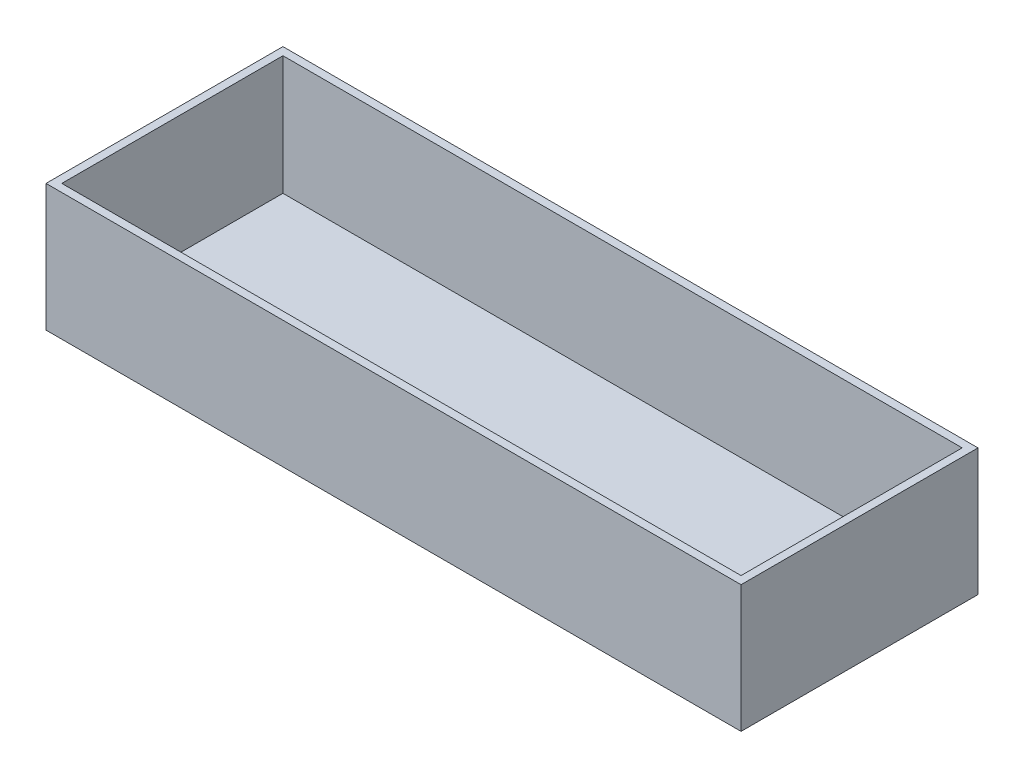
SolidWorks part; units mm, degrees
ref_plane "Front Plane" through (0, 0, 0) normal (0, 0, 1) x (1, 0, 0)
ref_plane "Top Plane" through (0, 0, 0) normal (0, 1, 0) x (1, 0, 0)
ref_plane "Right Plane" through (0, 0, 0) normal (1, 0, 0) x (0, 0, -1)
sketch "Sketch1" plane through (0, 0, 0) normal (0, 1, 0) x (1, 0, 0)
  line L1 (-139.7, -47.625) -> (139.7, -47.625)
  line L2 (-139.7, -47.625) -> (-139.7, 47.625)
  line L3 (-139.7, 47.625) -> (139.7, 47.625)
  line L4 (139.7, -47.625) -> (139.7, 47.625)
  line L5 (-139.7, -47.625) -> (139.7, 47.625) construction
  line L6 (-139.7, 47.625) -> (139.7, -47.625) construction
  point P0 (0, 0)
  dimension "D1" = 95.25
  dimension "D2" = 279.4
extrude "Boss-Extrude1" add sketch "Sketch1" along normal blind 3.175
sketch "Sketch2" plane through (0, 3.175, 0) normal (0, 1, 0) x (1, 0, 0)
  line L8 (136.525, -44.45) -> (136.525, 44.45)
  line L9 (136.525, 44.45) -> (-136.525, 44.45)
  line L10 (-136.525, 44.45) -> (-136.525, -44.45)
  line L11 (-136.525, -44.45) -> (136.525, -44.45)
  line L12 (136.525, -44.45) -> (136.525, 44.45)
  line L13 (136.525, 44.45) -> (-136.525, 44.45)
  line L14 (-136.525, 44.45) -> (-136.525, -44.45)
  line L15 (-136.525, -44.45) -> (136.525, -44.45)
  line L16 (139.7, -47.625) -> (139.7, 47.625)
  line L17 (139.7, 47.625) -> (-139.7, 47.625)
  line L18 (-139.7, 47.625) -> (-139.7, -47.625)
  line L19 (-139.7, -47.625) -> (139.7, -47.625)
  line L20 (139.7, -47.625) -> (139.7, 47.625)
  line L21 (139.7, 47.625) -> (-139.7, 47.625)
  line L22 (-139.7, 47.625) -> (-139.7, -47.625)
  line L23 (-139.7, -47.625) -> (139.7, -47.625)
  dimension "D1" = 3.175
  dimension "D2" = 0
extrude "Boss-Extrude2" add sketch "Sketch2" along normal blind 47.9044
